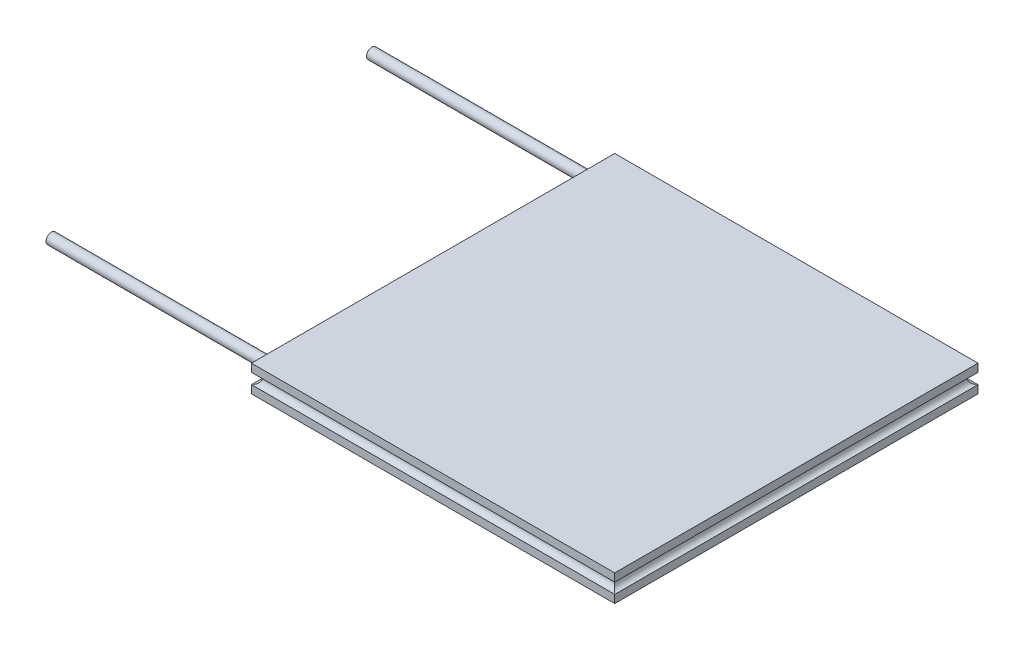
SolidWorks part; units mm, degrees
ref_plane "Front Plane" through (0, 0, 0) normal (0, 0, 1) x (1, 0, 0)
ref_plane "Top Plane" through (0, 0, 0) normal (0, 1, 0) x (1, 0, 0)
ref_plane "Right Plane" through (0, 0, 0) normal (1, 0, 0) x (0, 0, -1)
sketch "Sketch2" plane through (0, 0, 0) normal (0, 1, 0) x (1, 0, 0)
  line L1 (-20.5, -20.5) -> (20.5, -20.5)
  line L2 (-20.5, -20.5) -> (-20.5, 20.5)
  line L3 (-20.5, 20.5) -> (20.5, 20.5)
  line L4 (20.5, -20.5) -> (20.5, 20.5)
  line L5 (-20.5, -20.5) -> (20.5, 20.5) construction
  line L6 (-20.5, 20.5) -> (20.5, -20.5) construction
  point P0 (0, 0)
extrude "Boss-Extrude1" add sketch "Sketch2" along normal blind 3
sketch "Sketch3" plane through (-20.5, 0, 0) normal (-1, 0, 0) x (0, 0, 1)
  line L0 (0, 0) -> (0, 6.6126) construction
  circle A0 centre (-18.0878, 1.4962) radius 1
  circle A1 centre (18.0878, 1.4962) radius 1
extrude "Cut-Extrude1" cut sketch "Sketch3" against normal blind 0.2
sketch "Sketch4" plane through (-20.5, 0, 0) normal (-1, 0, 0) x (0, 0, 1)
  line L0 (-20.5, 3) -> (-20.5, 0) construction
  line L1 (20.5, 3) -> (20.5, 0) construction
  circle A0 centre (-20.5, 1.5) radius 0.6
  circle A1 centre (20.5, 1.5) radius 0.6
extrude "Cut-Extrude2" cut sketch "Sketch4" against normal up to surface (41 mm away) up to face at (20.5, 1.5, 0)
sketch "Sketch5" plane through (0, 0, 20.5) normal (0, 0, 1) x (1, 0, 0)
  line L0 (-20.5, 2.1) -> (-20.5, 0.9) construction
  line L1 (20.5, 0.9) -> (20.5, 2.1) construction
  circle A0 centre (-20.5, 1.5) radius 0.6
  circle A1 centre (20.5, 1.5) radius 0.6
extrude "Cut-Extrude3" cut sketch "Sketch5" against normal up to surface (41 mm away) up to face at (0, 2.55, -20.5)
sketch "Sketch6" plane through (-20.5, 0, 0) normal (-1, 0, 0) x (0, 0, 1)
  circle A0 centre (-18.0878, 1.4962) radius 0.6
  circle A1 centre (18.0878, 1.4962) radius 0.6
extrude "Boss-Extrude2" add sketch "Sketch6" along normal blind 25 and the other way blind 1
